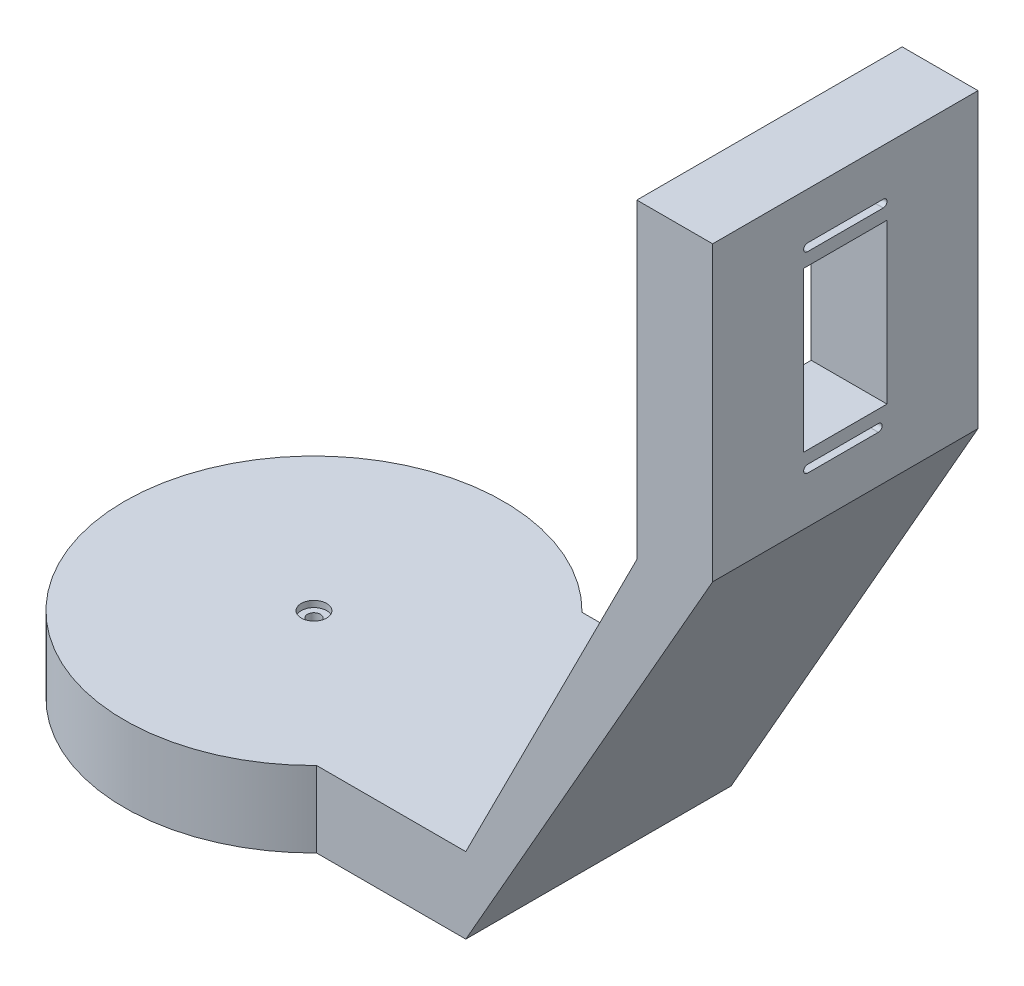
SolidWorks part; units mm, degrees
ref_plane "Front" through (0, 0, 0) normal (0, 0, 1) x (1, 0, 0)
ref_plane "Top" through (0, 0, 0) normal (0, 1, 0) x (1, 0, 0)
ref_plane "Right" through (0, 0, 0) normal (1, 0, 0) x (0, 0, -1)
sketch "草图1" plane through (0, 0, 0) normal (0, 1, 0) x (1, 0, 0)
  line L13 (0.0555, 35) -> (75.0555, 35)
  line L14 (0.0555, 35) -> (0.0555, -35)
  line L15 (0.0555, -35) -> (75.0555, -35)
  line L16 (75.0555, 35) -> (75.0555, -35)
  circle A1 centre (0, 0) radius 50
  dimension "D1" = 100
  dimension "D2" = 35
  dimension "D3" = 35
  dimension "D4" = 75
extrude "凸台-拉伸1" add sketch "草图1" along normal blind 20 contours A1 L15 L16 L13 | L15 A1 L13 L14 | L13 A1 L15 L14
sketch "草图2" plane through (0, 0, 35) normal (0, 0, 1) x (1, 0, 0)
  line L0 (75.0555, 0) -> (140.1741, 114.1921)
  line L1 (140.1741, 114.1921) -> (140.1741, 191.4116)
  line L2 (140.1741, 191.4116) -> (120.1741, 191.4116)
  line L3 (120.1741, 191.4116) -> (120.1741, 109.2863)
  line L5 (120.1741, 109.2863) -> (75.0555, 20)
  line L6 (75.0555, 20) -> (75.0555, 0)
  dimension "D1" = 20
  dimension "D2" = 77.2194
extrude "凸台-拉伸2" add sketch "草图2" against normal blind 70 contours L2 L3 L5 L6 L0 L1
hole_wizard "1/4 六角头螺钉的柱形沉头孔base" positions "草图7" profile "草图8" counterbore size "M3" standard "ANSI Metric" end condition through all
sketch "草图7" plane through (0, 20, 0) normal (0, 1, 0) x (1, 0, 0)
  point P0 (0, 0)
sketch "草图8" plane through (0, 20, 0) normal (1, 0, 0) x (0, 0, 1)
  line L0 (0, 0) -> (0, 20)
  line L1 (0, 20) -> (1.7, 20)
  line L3 (1.7, 20) -> (1.7, 1.65)
  line L4 (1.7, 1.65) -> (3.35, 1.65)
  line L5 (3.35, 1.65) -> (3.35, 0)
  line L7 (3.35, 0) -> (0, 0)
  line L11 (0, -6.35) -> (0, 107.95) construction
  dimension "通孔孔直径" = 3.4
  dimension "通孔孔深度" = 20
  dimension "柱形沉头孔直径" = 6.7
  dimension "柱形沉头孔深度" = 1.65
sketch "草图10" plane through (0, 0, 35) normal (0, 0, 1) x (1, 0, 0)
sketch "草图11" plane through (140.1741, 0, 0) normal (1, 0, 0) x (0, 0, -1)
  line L1 (-11, 173.8016) -> (11, 173.8016)
  line L2 (-11, 173.8016) -> (-11, 131.8016)
  line L3 (-11, 131.8016) -> (11, 131.8016)
  line L4 (11, 173.8016) -> (11, 131.8016)
  line L5 (-35, 114.1921) -> (-35, 191.4116) construction
  line L7 (35, 191.4116) -> (-35, 191.4116) construction
  dimension "D1" = 22
  dimension "D2" = 42
  dimension "D3" = 24
  dimension "D4" = 17.61
extrude "切除-拉伸1" cut sketch "草图11" against normal blind 32
sketch "草图14" plane through (140.1741, 0, 0) normal (1, 0, 0) x (0, 0, -1)
  line L0 (-10, 179.1016) -> (10, 179.1016)
  line L1 (-10, 177.1016) -> (10, 177.1016)
  line L2 (11, 173.8016) -> (-11, 173.8016) construction
  line L3 (-35, 114.1921) -> (-35, 191.4116) construction
  line L6 (-10, 128.5016) -> (8.7063, 128.5016)
  line L7 (-10, 126.5016) -> (8.7063, 126.5016)
  line L8 (-11, 131.8016) -> (11, 131.8016) construction
  arc A0 (-10, 179.1016) -> (-10, 177.1016) centre (-10, 178.1016) ccw
  arc A1 (10, 179.1016) -> (10, 177.1016) centre (10, 178.1016) cw
  arc A4 (-10, 128.5016) -> (-10, 126.5016) centre (-10, 127.5016) ccw
  arc A5 (8.7063, 128.5016) -> (8.7063, 126.5016) centre (8.7063, 127.5016) cw
  dimension "D3" = 25
  dimension "D4" = 3.3
  dimension "D1" = 2
  dimension "D2" = 3.3
  dimension "D5" = 25
extrude "切除-拉伸2" cut sketch "草图14" against normal blind 67
sketch "草图19" plane through (0, 0, 0) normal (0, -1, 0) x (1, 0, 0)
  line L0 (-29.939, 2.9835) -> (0, 6)
  line L1 (29.9255, 2.977) -> (0, 6)
  line L2 (29.8896, -3.02) -> (0, -6)
  line L3 (-30.0737, -4.2635) -> (0, -6)
  arc A2 (29.8896, -3.02) -> (29.9255, 2.977) centre (30, -0.022) ccw
  arc A3 (-30.0737, -4.2635) -> (-29.939, 2.9835) centre (-30, -0.6401) cw
  circle A4 centre (0, 0) radius 6
  dimension "D1" = 30
  dimension "D2" = 30
sketch "草图20" plane through (0, 0, 0) normal (0, -1, 0) x (1, 0, 0)
  line L0 (0, 6) -> (-10.4471, 4.9474)
  line L1 (-29.939, 2.9835) -> (0, 6) construction
  line L2 (-10.4471, 4.9474) -> (-10.4471, -5.3968)
  line L3 (-30.0737, -4.2635) -> (0, -6) construction
  line L4 (-10.4471, -5.3968) -> (0, -6)
  line L6 (0, -6) -> (10.4468, -4.9584)
  line L7 (29.8896, -3.02) -> (0, -6) construction
  line L8 (10.4468, -4.9584) -> (10.4468, 4.9447)
  line L9 (29.9255, 2.977) -> (0, 6) construction
  line L10 (10.4468, 4.9447) -> (0, 6)
  dimension "D1" = 10.5
  dimension "D2" = 10.5
extrude "切除-拉伸3" cut sketch "草图19" against normal blind 2 contours L1 L0 A3 L3 L2 A2
extrude "切除-拉伸4" cut sketch "草图20" against normal blind 3.5
